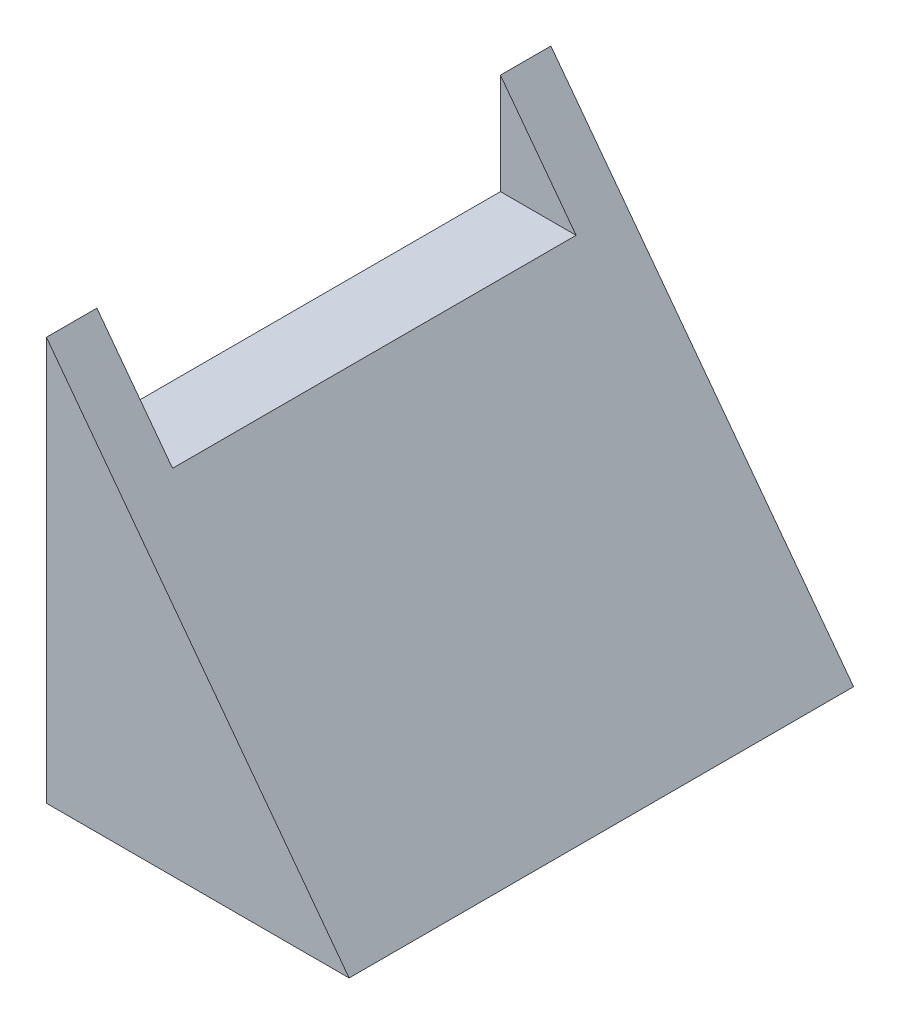
SolidWorks part; units mm, degrees
ref_plane "Front Plane" through (0, 0, 0) normal (0, 0, 1) x (1, 0, 0)
ref_plane "Top Plane" through (0, 0, 0) normal (0, 1, 0) x (1, 0, 0)
ref_plane "Right Plane" through (0, 0, 0) normal (1, 0, 0) x (0, 0, -1)
sketch "Sketch1" plane through (0, 0, 0) normal (0, 0, 1) x (1, 0, 0)
  line L0 (19.05, 0) -> (-19.05, 0)
  line L1 (-19.05, 0) -> (-19.05, 50.8)
  line L2 (-19.05, 50.8) -> (19.05, 0)
  point P0 (-52.6004, 101.9081)
  point P4 (0, 0)
  dimension "D1" = 90
  dimension "D2" = 50.8
  dimension "D3" = 38.1
extrude "Boss-Extrude1" add sketch "Sketch1" along normal blind 63.5
sketch "Sketch2" plane through (-19.05, 0, 0) normal (-1, 0, 0) x (0, 0, 1)
  line L0 (63.5, 50.8) -> (0, 50.8) construction
  line L1 (63.5, 0) -> (63.5, 50.8) construction
  line L2 (57.15, 50.8) -> (6.35, 50.8)
  line L3 (57.15, 50.8) -> (57.15, 38.1)
  line L4 (57.15, 38.1) -> (6.35, 38.1)
  line L5 (6.35, 50.8) -> (6.35, 38.1)
  line L6 (0, 0) -> (0, 50.8) construction
  dimension "D1" = 6.35
  dimension "D2" = 6.35
  dimension "D3" = 12.7
extrude "Cut-Extrude2" cut sketch "Sketch2" against normal through all
